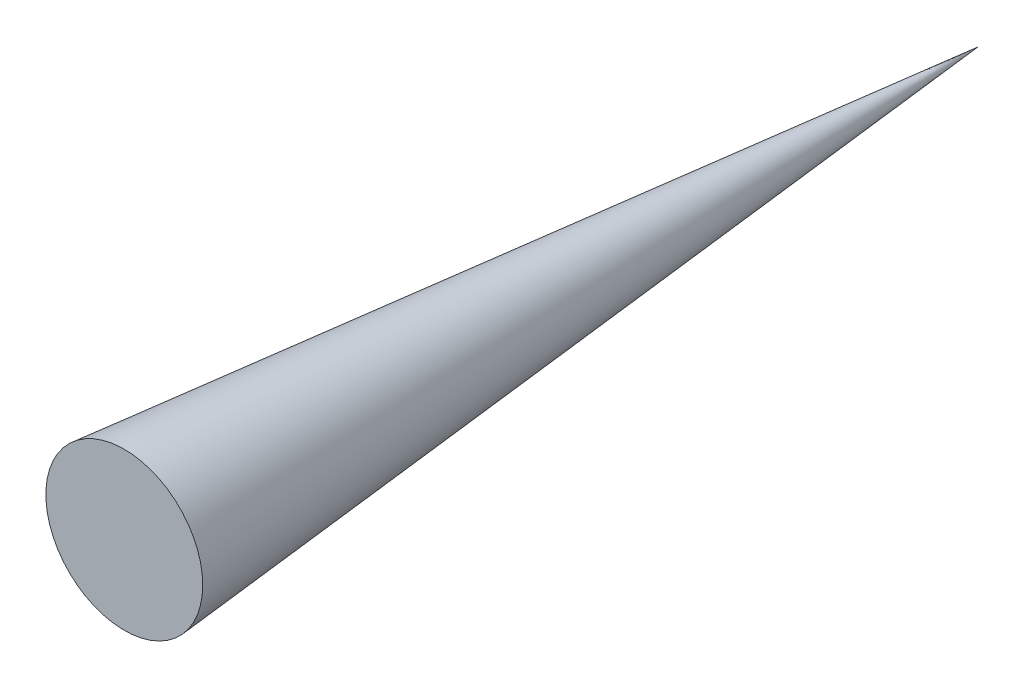
SolidWorks part; units mm, degrees
ref_plane "Front" through (0, 0, 0) normal (0, 0, 1) x (1, 0, 0)
ref_plane "Top" through (0, 0, 0) normal (0, 1, 0) x (1, 0, 0)
ref_plane "Right" through (0, 0, 0) normal (1, 0, 0) x (0, 0, -1)
sketch "Sketch1" plane through (0, 0, 0) normal (0, 1, 0) x (1, 0, 0)
  line L0 (0, 0) -> (-30, 0)
  line L1 (0, 0) -> (0, 326.5)
  line L2 (0, 326.5) -> (-30, 0)
  line L3 (0, -33.993) -> (0, 333.1348) construction
  dimension "D1" = 30
  dimension "D2" = 326.5
revolve "Revolve1" add sketch "Sketch1" angle 360 about L3
